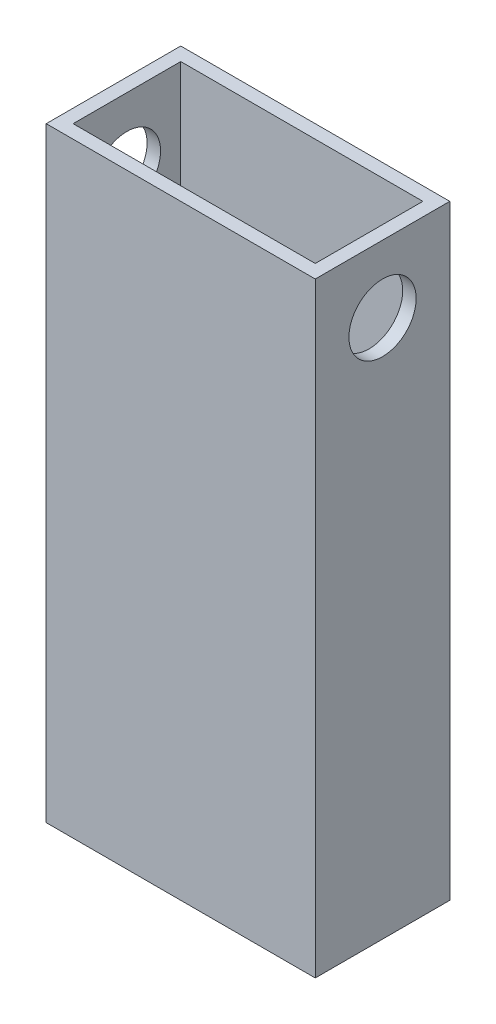
SolidWorks part; units mm, degrees
ref_plane "Front Plane" through (0, 0, 0) normal (0, 0, 1) x (1, 0, 0)
ref_plane "Top Plane" through (0, 0, 0) normal (0, 1, 0) x (1, 0, 0)
ref_plane "Right Plane" through (0, 0, 0) normal (1, 0, 0) x (0, 0, -1)
sketch "Sketch1" plane through (0, 0, 0) normal (0, 1, 0) x (1, 0, 0)
  line L1 (0, 0) -> (50.8, 0)
  line L2 (0, 0) -> (0, 25.4)
  line L3 (0, 25.4) -> (50.8, 25.4)
  line L4 (50.8, 0) -> (50.8, 25.4)
  dimension "D1" = 25.4
  dimension "D2" = 50.8
extrude "Extrude-Thin1" add sketch "Sketch1" along normal blind 114.3 thin thin type one direction reverse wall 2.54
sketch "Sketch2" plane through (50.8, 0, 0) normal (1, 0, 0) x (0, 0, -1)
  line L0 (12.7, 101.6) -> (12.7, 114.3) construction
  line L1 (0, 114.3) -> (25.4, 114.3) construction
  circle A0 centre (12.7, 101.6) radius 6.35
  dimension "D1" = 12.7
  dimension "D2" = 12.7
extrude "Cut-Extrude1" cut sketch "Sketch2" against normal through all
